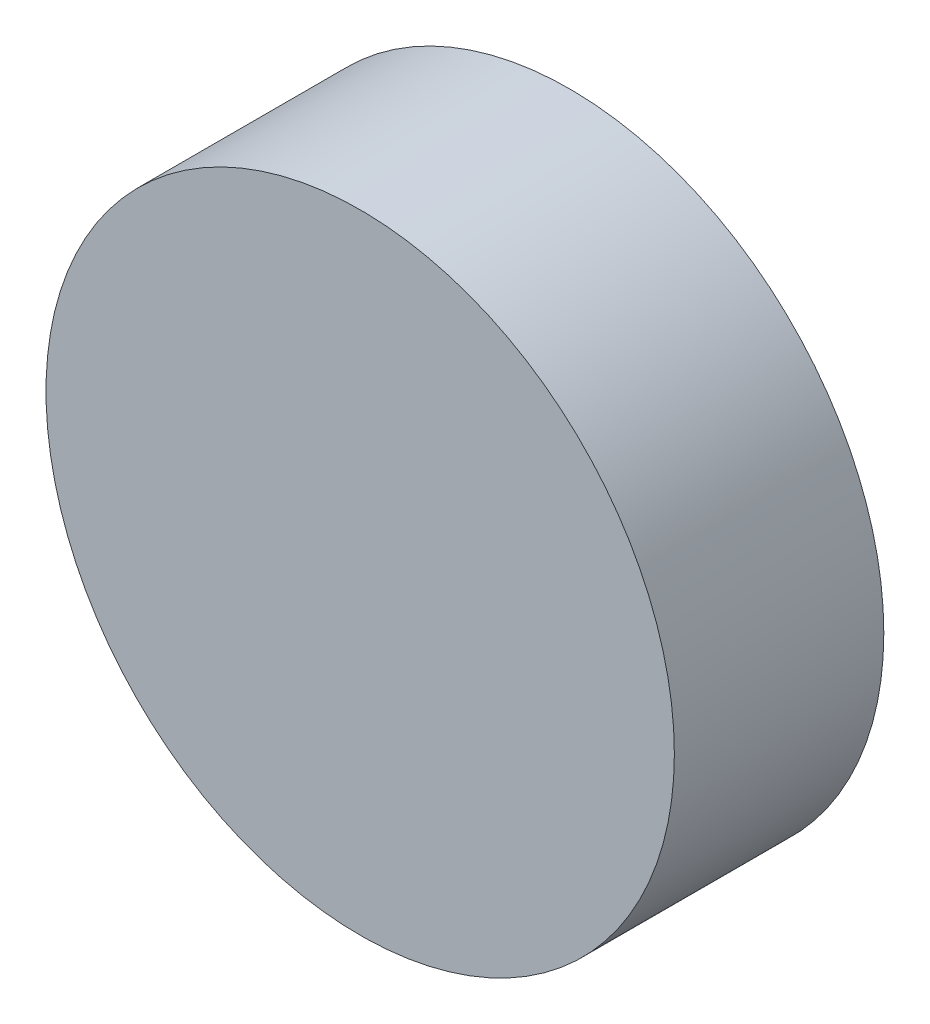
SolidWorks part; units mm, degrees
ref_plane "Front Plane" through (0, 0, 0) normal (0, 0, 1) x (1, 0, 0)
ref_plane "Top Plane" through (0, 0, 0) normal (0, 1, 0) x (1, 0, 0)
ref_plane "Right Plane" through (0, 0, 0) normal (1, 0, 0) x (0, 0, -1)
sketch "Sketch1" plane through (0, 0, 0) normal (0, 0, 1) x (1, 0, 0)
  circle A0 centre (0, 0) radius 15
  dimension "D1" = 30
extrude "Boss-Extrude1" add sketch "Sketch1" along normal blind 10
